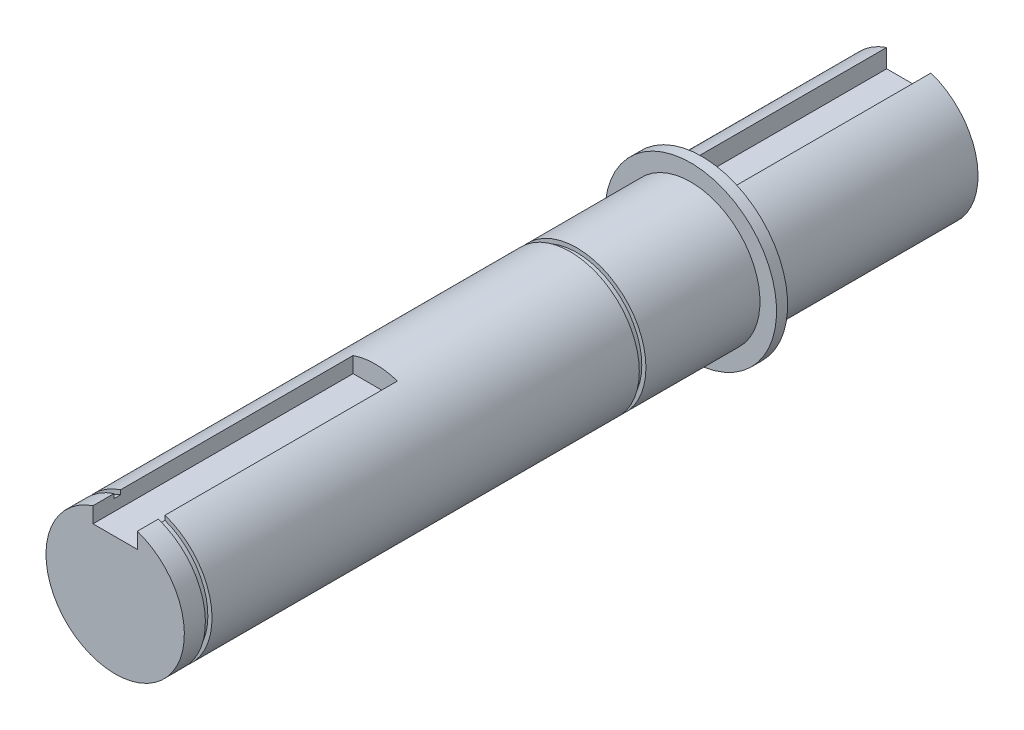
SolidWorks part; units mm, degrees
material "Plain Carbon Steel"
ref_plane "Front Plane" through (0, 0, 0) normal (0, 0, 1) x (1, 0, 0)
ref_plane "Top Plane" through (0, 0, 0) normal (0, 1, 0) x (1, 0, 0)
ref_plane "Right Plane" through (0, 0, 0) normal (1, 0, 0) x (0, 0, -1)
sketch "Sketch1" plane through (0, 0, 0) normal (0, 0, 1) x (1, 0, 0)
  circle A0 centre (0, 0) radius 12.5
  dimension "D1" = 25
extrude "Boss-Extrude1" add sketch "Sketch1" along normal blind 143.4
sketch "Sketch4" plane through (0, 0, 0) normal (0, 0, -1) x (-1, 0, 0)
  line L0 (0, 55) -> (0, -55) construction
  line L1 (-4, 8.5) -> (4, 8.5)
  line L2 (-4, 8.5) -> (-4, 16.5)
  line L3 (-4, 16.5) -> (4, 16.5)
  line L4 (4, 8.5) -> (4, 16.5)
  line L5 (-4, 8.5) -> (4, 16.5) construction
  line L6 (-4, 16.5) -> (4, 8.5) construction
  circle A0 centre (0, 0) radius 12.5 construction
  point P0 (0, 12.5)
  dimension "D1" = 8
  dimension "D2" = 8
extrude "Cut-Extrude1" cut sketch "Sketch4" against normal blind 35.4
ref_plane "Plane1" through (0, 0, 37.4) normal (0, 0, -1) x (-1, 0, 0)
sketch "Sketch11" plane through (0, 0, 37.4) normal (0, 0, -1) x (-1, 0, 0)
  circle A0 centre (0, 0) radius 15.5
  dimension "D1" = 31
extrude "Boss-Extrude4" add sketch "Sketch11" against normal blind 2
ref_plane "Plane2" through (0, 0, 60) normal (0, 0, 1) x (1, 0, 0)
sketch "Sketch12" plane through (0, 0, 60) normal (0, 0, 1) x (1, 0, 0)
  circle A0 centre (0, 0) radius 12.5
  circle A1 centre (0, 0) radius 11.75
  dimension "D1" = 25
  dimension "D2" = 23.5
extrude "Cut-Extrude2" cut sketch "Sketch12" along normal blind 1.2
sketch "Sketch13" plane through (0, 0, 143.4) normal (0, 0, 1) x (1, 0, 0)
  line L1 (-4, 9) -> (4, 9)
  line L2 (-4, 9) -> (-4, 16)
  line L3 (-4, 16) -> (4, 16)
  line L4 (4, 9) -> (4, 16)
  line L5 (-4, 9) -> (4, 16) construction
  line L6 (-4, 16) -> (4, 9) construction
  circle A0 centre (0, 0) radius 12.5 construction
  point P0 (0, 12.5)
  dimension "D1" = 8
  dimension "D2" = 7
extrude "Cut-Extrude3" cut sketch "Sketch13" against normal blind 47
ref_plane "Plane4" through (0, 0, 138.4) normal (0, 0, 1) x (1, 0, 0)
sketch "Sketch16" plane through (0, 0, 138.4) normal (0, 0, 1) x (1, 0, 0)
  circle A0 centre (0, 0) radius 12.5
  circle A1 centre (0, 0) radius 11.75
  dimension "D1" = 25
  dimension "D2" = 23.5
extrude "Cut-Extrude5" cut sketch "Sketch16" along normal blind 1.2 contours A1 | A0
